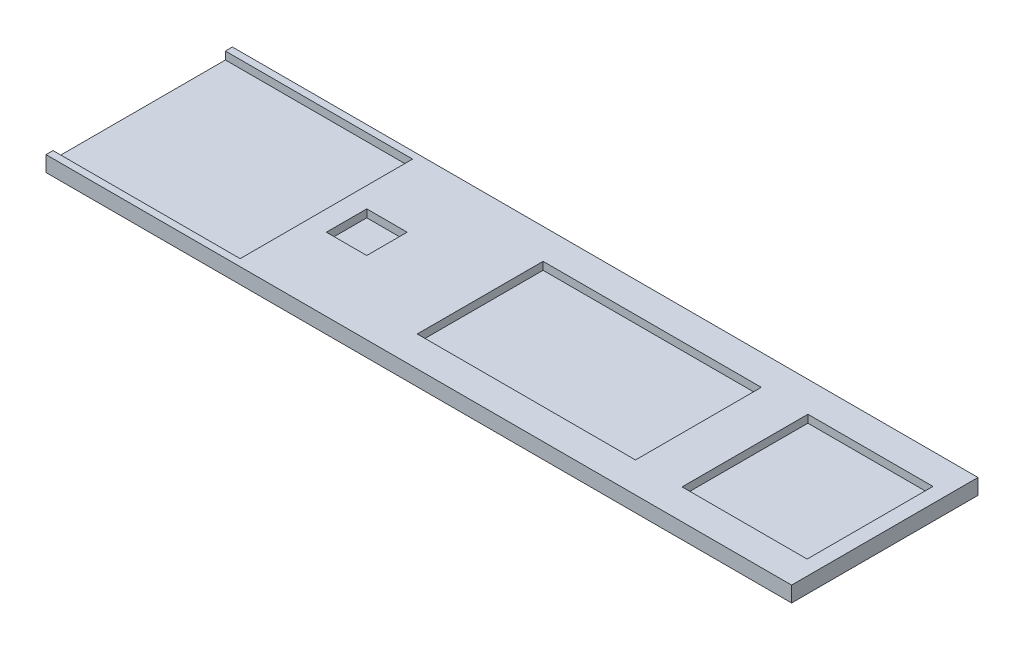
SolidWorks part; units mm, degrees
ref_plane "Front Plane" through (0, 0, 0) normal (0, 0, 1) x (1, 0, 0)
ref_plane "Top Plane" through (0, 0, 0) normal (0, 1, 0) x (1, 0, 0)
ref_plane "Right Plane" through (0, 0, 0) normal (1, 0, 0) x (0, 0, -1)
sketch "Sketch1" plane through (0, 0, 0) normal (0, 1, 0) x (1, 0, 0)
  line L1 (-4.5409, 57.6868) -> (235.4591, 57.6868)
  line L2 (-4.5409, 57.6868) -> (-4.5409, -2.3132)
  line L3 (-4.5409, -2.3132) -> (235.4591, -2.3132)
  line L4 (235.4591, 57.6868) -> (235.4591, -2.3132)
  dimension "D1" = 60
  dimension "D2" = 240
extrude "Boss-Extrude1" add sketch "Sketch1" along normal blind 5
sketch "Sketch5" plane through (0, 5, 0) normal (0, 1, 0) x (1, 0, 0)
  line L0 (235.4591, 57.6868) -> (-4.5409, 57.6868) construction
  line L1 (190.4591, 47.9368) -> (230.7091, 47.9368)
  line L2 (190.4591, 47.9368) -> (190.4591, 7.4368)
  line L3 (190.4591, 7.4368) -> (230.7091, 7.4368)
  line L4 (230.7091, 47.9368) -> (230.7091, 7.4368)
  line L5 (-4.5409, 57.6868) -> (-4.5409, -2.3132) construction
  line L6 (235.4591, -2.3132) -> (235.4591, 57.6868) construction
  line L7 (105.2091, 47.9368) -> (175.4591, 47.9368)
  line L8 (105.2091, 47.9368) -> (105.2091, 7.4368)
  line L9 (105.2091, 7.4368) -> (175.4591, 7.4368)
  line L10 (175.4591, 47.9368) -> (175.4591, 7.4368)
  line L11 (-4.5409, -2.3132) -> (235.4591, -2.3132) construction
  line L12 (62.2091, 34.1868) -> (75.2091, 34.1868)
  line L13 (62.2091, 34.1868) -> (62.2091, 21.1868)
  line L14 (62.2091, 21.1868) -> (75.2091, 21.1868)
  line L15 (75.2091, 34.1868) -> (75.2091, 21.1868)
  line L17 (-4.5409, 55.4368) -> (55.7091, 55.4368)
  line L18 (-4.5409, 55.4368) -> (-4.5409, -0.0632)
  line L19 (-4.5409, -0.0632) -> (55.7091, -0.0632)
  line L20 (55.7091, 55.4368) -> (55.7091, -0.0632)
  dimension "D1" = 40.25
  dimension "D2" = 40.5
  dimension "D3" = 9.75
  dimension "D4" = 195
  dimension "D5" = 70.25
  dimension "D6" = 40.5
  dimension "D7" = 15
  dimension "D8" = 9.75
  dimension "D9" = 130.25
  dimension "D10" = 13
  dimension "D11" = 13
  dimension "D12" = 23.5
  dimension "D13" = 30
  dimension "D14" = 60.25
  dimension "D15" = 55.5
  dimension "D16" = 2.25
extrude "Cut-Extrude1" cut sketch "Sketch5" against normal blind 2.5
